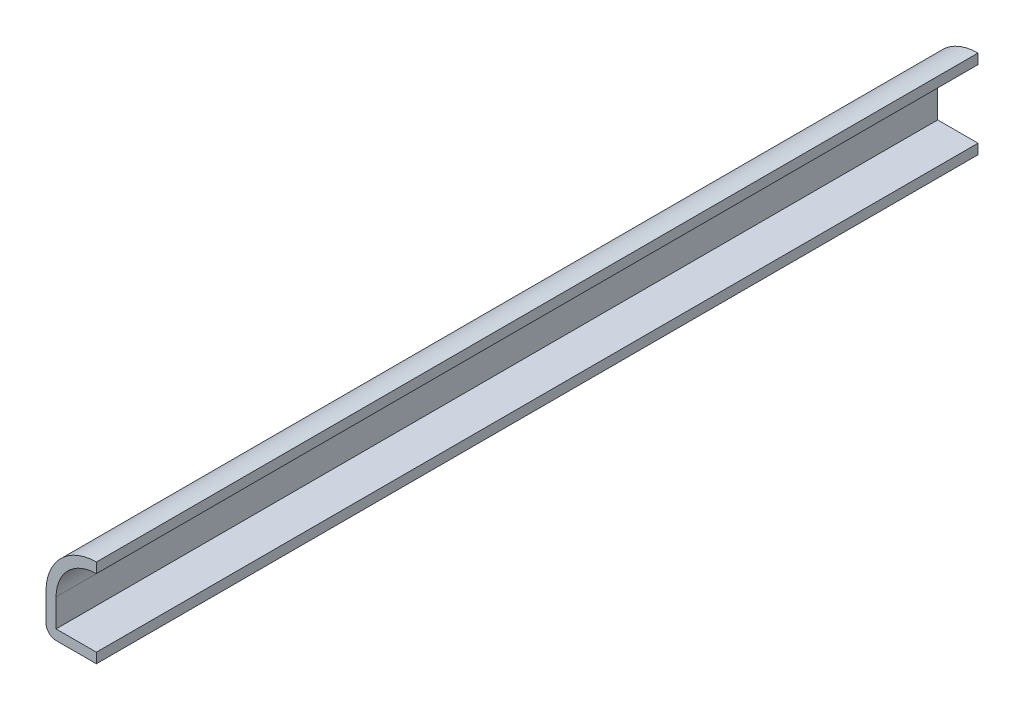
SolidWorks part; units mm, degrees
ref_plane "Front Plane" through (0, 0, 0) normal (0, 0, 1) x (1, 0, 0)
ref_plane "Top Plane" through (0, 0, 0) normal (0, 1, 0) x (1, 0, 0)
ref_plane "Right Plane" through (0, 0, 0) normal (1, 0, 0) x (0, 0, -1)
sketch "Sketch1" plane through (0, 0, 0) normal (0, 0, 1) x (1, 0, 0)
  line L3 (0, 0) -> (-6.35, 0)
  line L4 (-6.35, 0) -> (-6.35, 4.7625)
  line L5 (0, 11.1125) -> (0, 0) construction
  arc A1 (-6.35, 4.7625) -> (0, 11.1125) centre (0, 4.7625) cw
  point P6 (0, 0)
  dimension "D1" = 6.35
  dimension "D2" = 11.1125
extrude "Extrude-Thin1" add sketch "Sketch1" against normal blind 111.125 thin
fillet "Fillet1" radius 1.27 1 edges at (-6.35, 0, -55.5625)
